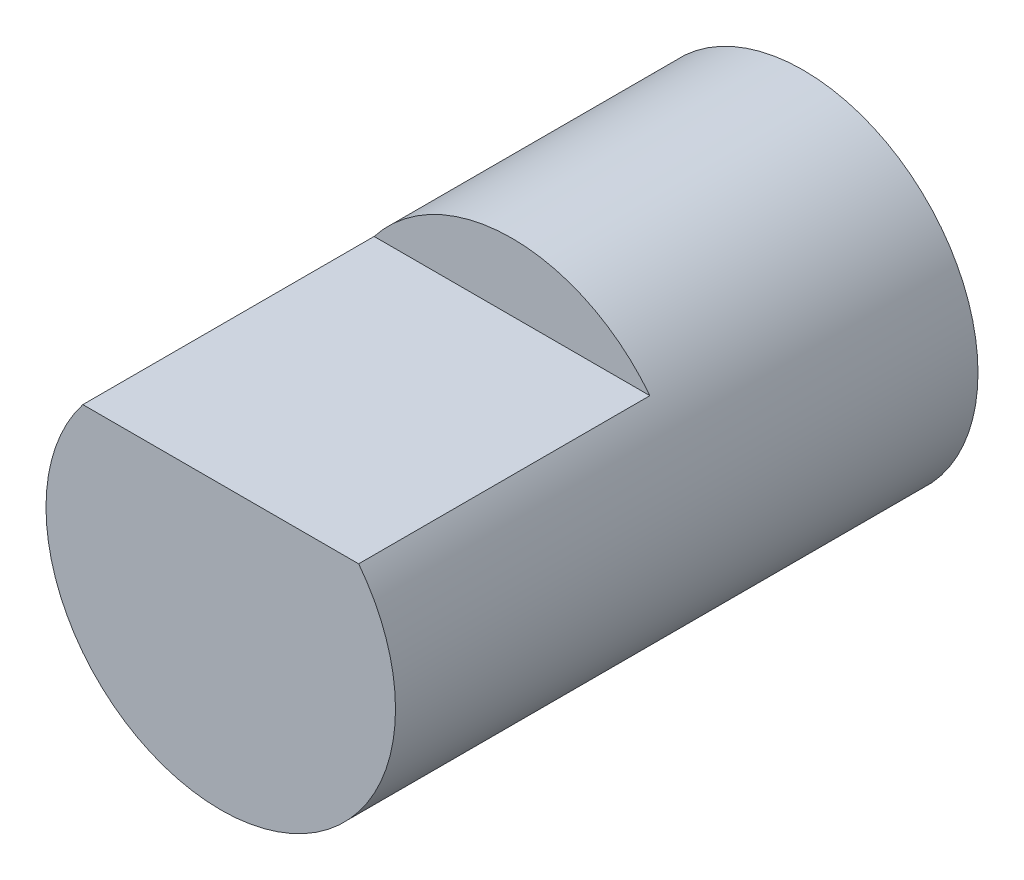
SolidWorks part; units mm, degrees
ref_plane "Alzado" through (0, 0, 0) normal (0, 0, 1) x (1, 0, 0)
ref_plane "Planta" through (0, 0, 0) normal (0, 1, 0) x (1, 0, 0)
ref_plane "Vista lateral" through (0, 0, 0) normal (1, 0, 0) x (0, 0, -1)
sketch "Croquis1" plane through (0, 0, 0) normal (0, 0, 1) x (1, 0, 0)
  circle A0 centre (0, 0) radius 3
extrude "Saliente-Extruir1" add sketch "Croquis1" along normal blind 10 contours A0
sketch "Croquis2" plane through (0, 0, 10) normal (0, 0, 1) x (1, 0, 0)
  line L0 (-2.3673, 1.8428) -> (2.3673, 1.8428)
  circle A0 centre (0, 0) radius 3 construction
  arc A1 (-2.3673, 1.8428) -> (2.3673, 1.8428) centre (0, 0) cw
extrude "Cortar-Extruir1" cut sketch "Croquis2" against normal blind 5 contours A1 L0
